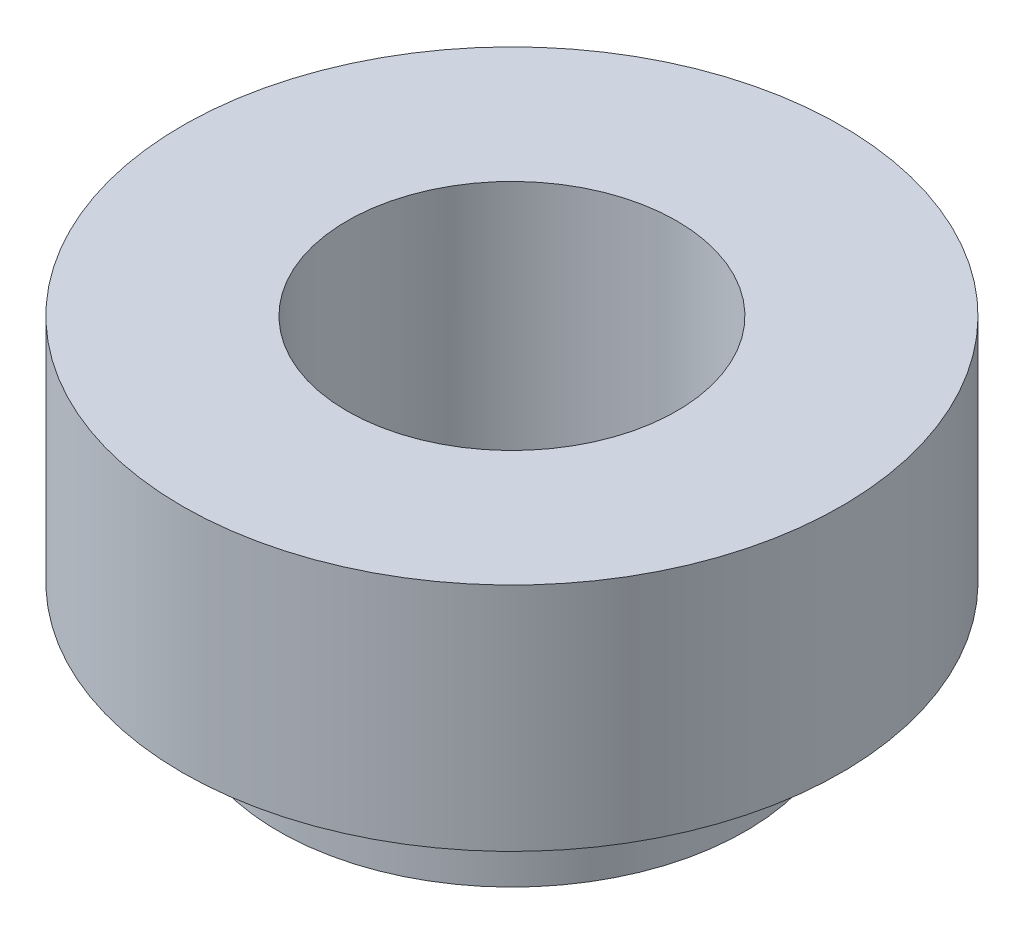
SolidWorks part; units mm, degrees
material "AISI 1015 鋼, 冷間引抜 (SS)"
ref_plane "正面" through (0, 0, 0) normal (0, 0, 1) x (1, 0, 0)
ref_plane "平面" through (0, 0, 0) normal (0, 1, 0) x (1, 0, 0)
ref_plane "右側面" through (0, 0, 0) normal (1, 0, 0) x (0, 0, -1)
sketch "ｽｹｯﾁ1" plane through (0, 0, 0) normal (0, 1, 0) x (1, 0, 0)
  circle A0 centre (0, 0) radius 3
  dimension "D1" = 6
extrude "ﾎﾞｽ - 押し出し1" add sketch "ｽｹｯﾁ1" along normal blind 2.1
sketch "ｽｹｯﾁ3" plane through (0, 0, 0) normal (0, -1, 0) x (-1, 0, 0)
  circle A0 centre (0, 0) radius 2.125
  dimension "D1" = 4.25
extrude "ﾎﾞｽ - 押し出し2" add sketch "ｽｹｯﾁ3" along normal blind 0.9
sketch "ｽｹｯﾁ4" plane through (0, -0.9, 0) normal (0, -1, 0) x (-1, 0, 0)
  circle A0 centre (0, 0) radius 1.5
  dimension "D1" = 3
extrude "ｶｯﾄ - 押し出し1" cut sketch "ｽｹｯﾁ4" against normal blind 3.3
